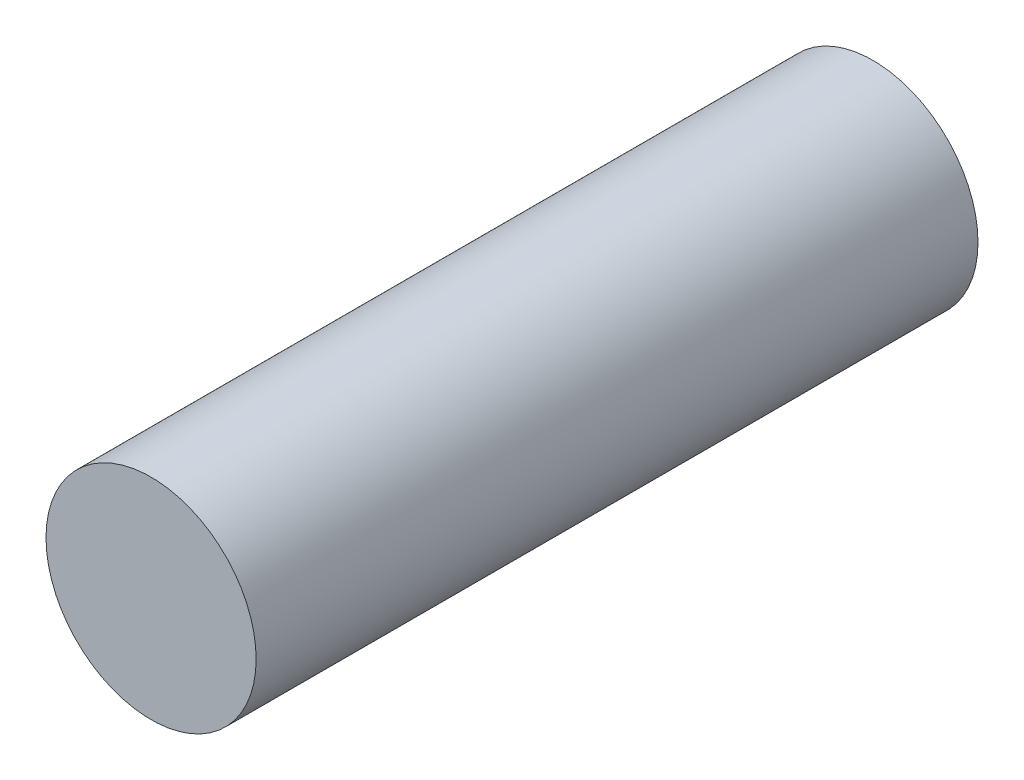
SolidWorks part; units mm, degrees
material "1023 Carbon Steel Sheet (SS)"
ref_plane "Front Plane" through (0, 0, 0) normal (0, 0, 1) x (1, 0, 0)
ref_plane "Top Plane" through (0, 0, 0) normal (0, 1, 0) x (1, 0, 0)
ref_plane "Right Plane" through (0, 0, 0) normal (1, 0, 0) x (0, 0, -1)
sketch "Sketch1" plane through (0, 0, 0) normal (0, 0, 1) x (1, 0, 0)
  circle A0 centre (0, 0) radius 2.5
  dimension "D1" = 5
extrude "Boss-Extrude1" add sketch "Sketch1" along normal up to surface (17.175 mm away)
equation "\"keelOutDiameter\"= 1in"
equation "\"keelInDiameter\"= \"keelOutDiameter\" - 0.125in"
equation "\"frontBoltClearance\"= 7.25mm"
equation "\"betweenBoltsDistance\"= 20mm"
equation "\"wingLength\"= 1.4m"
equation "\"frontTubeLength\"= \"wingLength\" / sin ( 34.95deg )"
equation "\"plateThickness\"= 5mm"
equation "\"crossBarOutDiameter\"= 1in"
equation "\"crossBarInDiameter\"= \"crossBarOutDiameter\" - 0.125in"
equation "\"frontToCrossBar\"= 466mm"
equation "\"cablePinDiameter\"= 5mm"
equation "\"D1@Sketch1\"=\"cablePinDiameter\""
